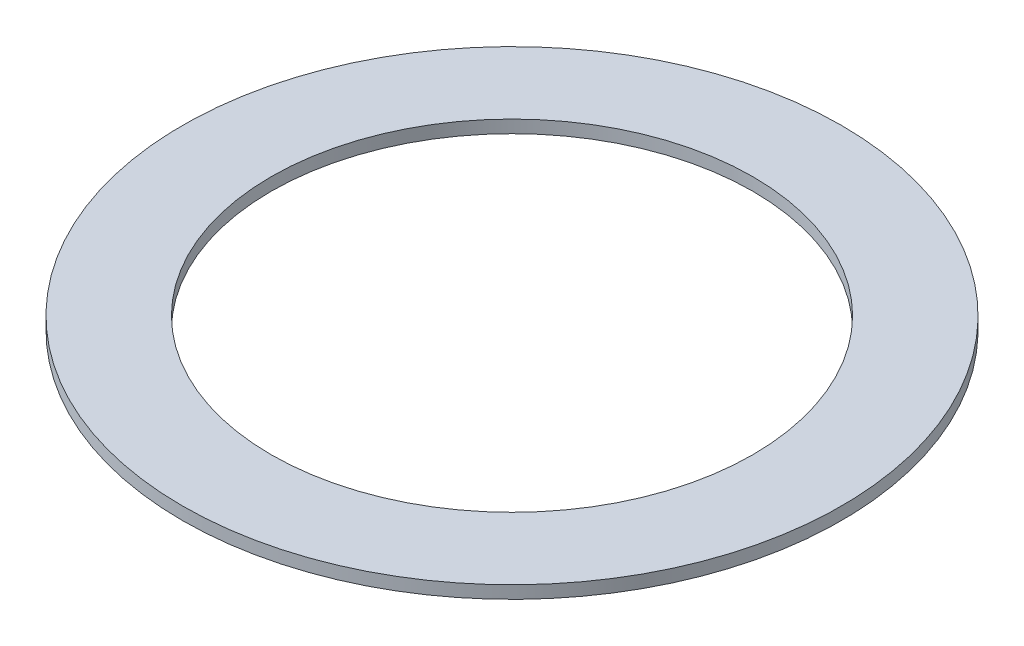
SolidWorks part; units mm, degrees
material "Alloy Steel"
ref_plane "X-Y Datum" through (0, 0, 0) normal (0, 0, 1) x (1, 0, 0)
ref_plane "X-Z Datum" through (0, 0, 0) normal (0, 1, 0) x (1, 0, 0)
ref_plane "Y-Z Datum" through (0, 0, 0) normal (1, 0, 0) x (0, 0, -1)
sketch "Sketch1" plane through (0, 0, 0) normal (0, 1, 0) x (1, 0, 0)
  circle A0 centre (0, 0) radius 9.5
  circle A1 centre (0, 0) radius 13
  dimension "D1" = 19
  dimension "D2" = 26
extrude "Boss-Extrude1" add sketch "Sketch1" along normal blind 0.5
